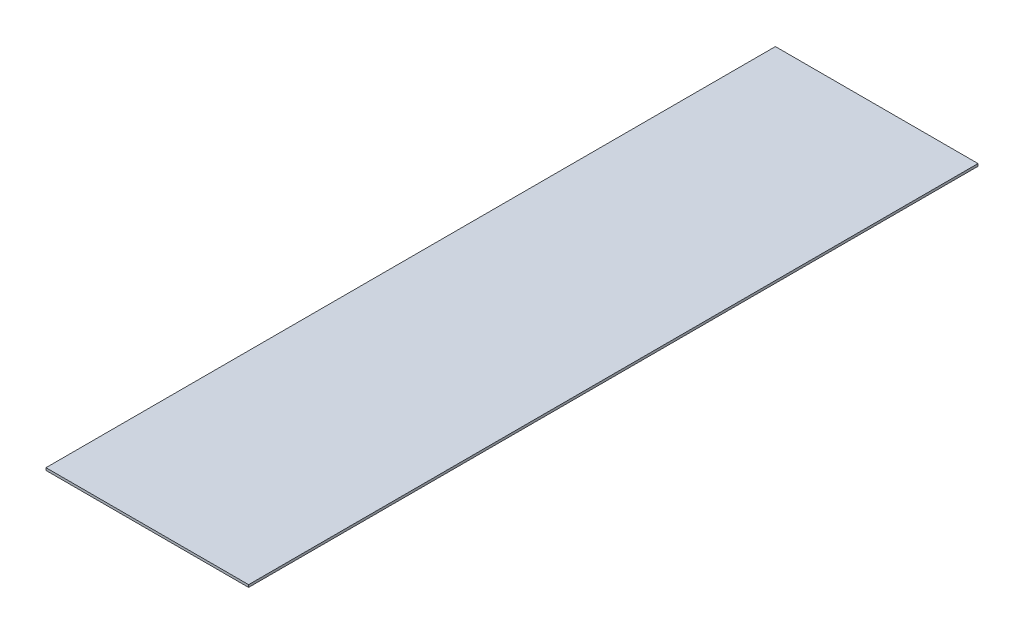
SolidWorks part; units mm, degrees
ref_plane "정면" through (0, 0, 0) normal (0, 0, 1) x (1, 0, 0)
ref_plane "윗면" through (0, 0, 0) normal (0, 1, 0) x (1, 0, 0)
ref_plane "우측면" through (0, 0, 0) normal (1, 0, 0) x (0, 0, -1)
sketch "스케치1" plane through (0, 0, 0) normal (0, 0, 1) x (1, 0, 0)
  line L1 (0, 0) -> (250, 0)
  line L2 (0, 0) -> (0, 3)
  line L3 (0, 3) -> (250, 3)
  line L4 (250, 0) -> (250, 3)
  dimension "D1" = 250
  dimension "D2" = 3
extrude "보스-돌출1" add sketch "스케치1" along normal blind 900
